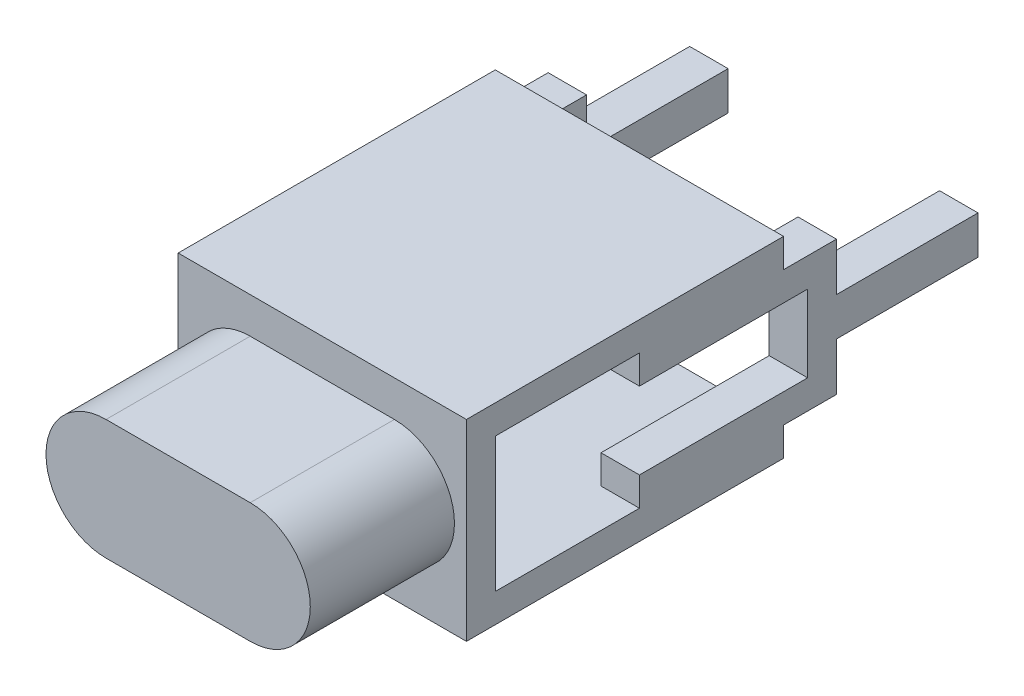
SolidWorks part; units mm, degrees
ref_plane "前视基准面" through (0, 0, 0) normal (0, 0, 1) x (1, 0, 0)
ref_plane "上视基准面" through (0, 0, 0) normal (0, 1, 0) x (1, 0, 0)
ref_plane "右视基准面" through (0, 0, 0) normal (1, 0, 0) x (0, 0, -1)
sketch "草图1" plane through (0, 0, 0) normal (0, 0, 1) x (1, 0, 0)
  circle A0 centre (0, 0) radius 7
extrude "凸台-拉伸1" add sketch "草图1" along normal blind 160 and the other way blind 36
sketch "草图2" plane through (0, 0, -36) normal (0, 0, -1) x (-1, 0, 0)
  line L0 (15, 12.5) -> (20, 7.5)
  line L1 (-20, 12.5) -> (20, 12.5)
  line L2 (-20, 12.5) -> (-20, -12.5)
  line L3 (-20, -12.5) -> (20, -12.5)
  line L4 (20, 12.5) -> (20, -12.5)
  line L5 (-20, 12.5) -> (20, -12.5) construction
  line L6 (-20, -12.5) -> (20, 12.5) construction
  line L7 (-15, 12.5) -> (-20, 7.5)
  line L8 (-20, -7.5) -> (-15, -12.5)
  line L9 (-15, -12.5) -> (15, -12.5)
  line L10 (15, -12.5) -> (20, -7.5)
  point P0 (0, 0)
  circle M1 centre (0, 0) radius 7
  dimension "D1" = 25
  dimension "D2" = 40
  dimension "D3" = 5
  dimension "D4" = 5
  dimension "D5" = 5
  dimension "D6" = 5
  dimension "D7" = 5
  dimension "D8" = 5
  dimension "D9" = 5
  dimension "D10" = 5
extrude "凸台-拉伸2" add sketch "草图2" along normal blind 8 contours L3 L10 L4 L0 L1 L7 L2 L8 M1 | M1
sketch "草图3" plane through (0, 0, -44) normal (0, 0, -1) x (-1, 0, 0)
  line L1 (9, 5.5) -> (-9, 5.5)
  line L2 (9, 5.5) -> (9, -5.5)
  line L3 (9, -5.5) -> (-9, -5.5)
  line L4 (-9, 5.5) -> (-9, -5.5)
  line L5 (9, 5.5) -> (-9, -5.5) construction
  line L6 (9, -5.5) -> (-9, 5.5) construction
  point P0 (0, 0)
  dimension "D1" = 18
  dimension "D2" = 11
extrude "凸台-拉伸3" add sketch "草图3" along normal blind 15
sketch "草图4" plane through (0, 0, -59) normal (0, 0, -1) x (-1, 0, 0)
  line L1 (15, 12.5) -> (-15, 12.5)
  line L2 (15, 12.5) -> (15, -12.5)
  line L3 (15, -12.5) -> (-15, -12.5)
  line L4 (-15, 12.5) -> (-15, -12.5)
  line L5 (15, 12.5) -> (-15, -12.5) construction
  line L6 (15, -12.5) -> (-15, 12.5) construction
  circle A0 centre (15, 0) radius 12.5
  circle A1 centre (-15, 0) radius 12.5
  point P0 (0, 0)
  line M1 (-9, 5.5) -> (-9, -5.5)
  line M2 (-9, -5.5) -> (9, -5.5)
  line M3 (9, -5.5) -> (9, 5.5)
  line M4 (9, 5.5) -> (-9, 5.5)
  dimension "D1" = 25
  dimension "D2" = 30
extrude "凸台-拉伸4" add sketch "草图4" along normal blind 30 contours L4 A1 | A1 L4 M4 M2 M1 | A1 M2 M4 M1 | A1 A0 M2 M4 | A0 M4 M2 M3 | L2 A0 M4 M3 M2 | L2 A0 | A1 L3 A0 M2 | A1 A0 L1 M4
sketch "草图5" plane through (0, 0, -89) normal (0, 0, -1) x (-1, 0, 0)
  line L1 (30, 20) -> (-30, 20)
  line L2 (30, 20) -> (30, -20)
  line L3 (30, -20) -> (-30, -20)
  line L4 (-30, 20) -> (-30, -20)
  line L5 (30, 20) -> (-30, -20) construction
  line L6 (30, -20) -> (-30, 20) construction
  point P0 (0, 0)
  dimension "D1" = 60
  dimension "D2" = 40
extrude "凸台-拉伸5" add sketch "草图5" along normal blind 6
sketch "草图6" plane through (0, 0, -95) normal (0, 0, -1) x (-1, 0, 0)
  line L0 (-30, 20) -> (-30, -20) construction
  line L1 (30, 20) -> (-30, 20)
  line L2 (30, 20) -> (30, 14)
  line L3 (30, 14) -> (-30, 14)
  line L4 (-30, 20) -> (-30, 14)
  line L5 (30, -20) -> (30, 20) construction
  line L6 (-30, -20) -> (30, -20)
  line L7 (-30, -20) -> (-30, -14)
  line L8 (-30, -14) -> (30, -14)
  line L9 (30, -20) -> (30, -14)
  dimension "D1" = 6
  dimension "D2" = 6
extrude "凸台-拉伸6" add sketch "草图6" along normal blind 60
sketch "草图7" plane through (-30, 0, 0) normal (-1, 0, 0) x (0, 0, 1)
  line L0 (-155, 14) -> (-95, 14) construction
  line L1 (-125, 14) -> (-160, 14)
  line L2 (-125, 14) -> (-125, 8)
  line L3 (-125, 8) -> (-160, 8)
  line L4 (-160, 14) -> (-160, 8)
  line L5 (-155, -14) -> (-95, -14) construction
  line L6 (-125, -14) -> (-160, -14)
  line L7 (-125, -14) -> (-125, -8)
  line L8 (-125, -8) -> (-160, -8)
  line L9 (-160, -14) -> (-160, -8)
  line L11 (-160, 14) -> (-166, 14)
  line L12 (-160, 14) -> (-160, -14)
  line L13 (-160, -14) -> (-166, -14)
  line L14 (-166, 14) -> (-166, -14)
  line L15 (-166, 0) -> (-195.4559, 0)
  line L16 (-166, 0) -> (-166, 4)
  line L17 (-166, 4) -> (-195.4559, 4)
  line L18 (-195.4559, 0) -> (-195.4559, 4)
  line L19 (-166, 0) -> (-195.4559, 0)
  line L20 (-166, 0) -> (-166, -4)
  line L21 (-166, -4) -> (-195.4559, -4)
  line L22 (-195.4559, 0) -> (-195.4559, -4)
  line M4 (-155, 14) -> (-95, 14)
  line M6 (-95, -14) -> (-155, -14)
  dimension "D1" = 6
  dimension "D2" = 6
  dimension "D3" = 6
  dimension "D4" = 35
  dimension "D5" = 4
  dimension "D6" = 4
extrude "凸台-拉伸7" add sketch "草图7" against normal blind 8 contours L1 L4 L3 L2 M4 | L9 L6 L7 L8 M6 | L11 L14 L13 L9 L12 L4 | L15 L22 L21 L14 | L18 L15 L14 L17
pattern_linear "阵列(线性)1" count 2 spacing 52 along (1, 0, 0) of "凸台-拉伸7"
sketch "草图8" plane through (0, 0, -59) normal (0, 0, 1) x (1, 0, 0)
  line L1 (-35.7833, 20.9794) -> (35.7833, 20.9794)
  line L2 (-35.7833, 20.9794) -> (-35.7833, -20.9794)
  line L3 (-35.7833, -20.9794) -> (35.7833, -20.9794)
  line L4 (35.7833, 20.9794) -> (35.7833, -20.9794)
  line L5 (-35.7833, 20.9794) -> (35.7833, -20.9794) construction
  line L6 (-35.7833, -20.9794) -> (35.7833, 20.9794) construction
  point P0 (0, 0)
extrude "切除-拉伸1" cut sketch "草图8" along normal blind 300
